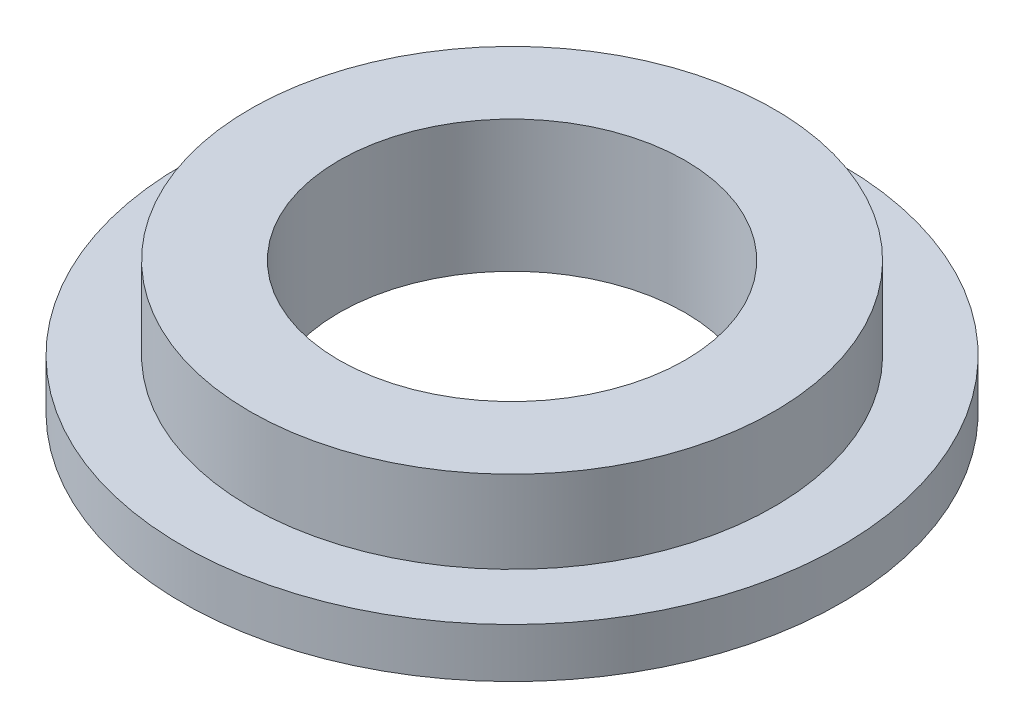
SolidWorks part; units mm, degrees
ref_plane "前视基准面" through (0, 0, 0) normal (0, 0, 1) x (1, 0, 0)
ref_plane "上视基准面" through (0, 0, 0) normal (0, 1, 0) x (1, 0, 0)
ref_plane "右视基准面" through (0, 0, 0) normal (1, 0, 0) x (0, 0, -1)
other "Configuration Table"
sketch "草图1" plane through (0, 0, 0) normal (0, 1, 0) x (1, 0, 0)
  circle A0 centre (0, 0) radius 10.5
  circle A1 centre (0, 0) radius 15.9
  dimension "D1" = 21
  dimension "D2" = 31.8
extrude "凸台-拉伸1" add sketch "草图1" along normal blind 5
sketch "草图2" plane through (0, 0, 0) normal (0, -1, 0) x (1, 0, 0)
  circle A0 centre (0, 0) radius 20
  circle A1 centre (0, 0) radius 10.5 construction
  circle A2 centre (0, 0) radius 10.5
  dimension "D1" = 40
extrude "凸台-拉伸2" add sketch "草图2" along normal blind 3
